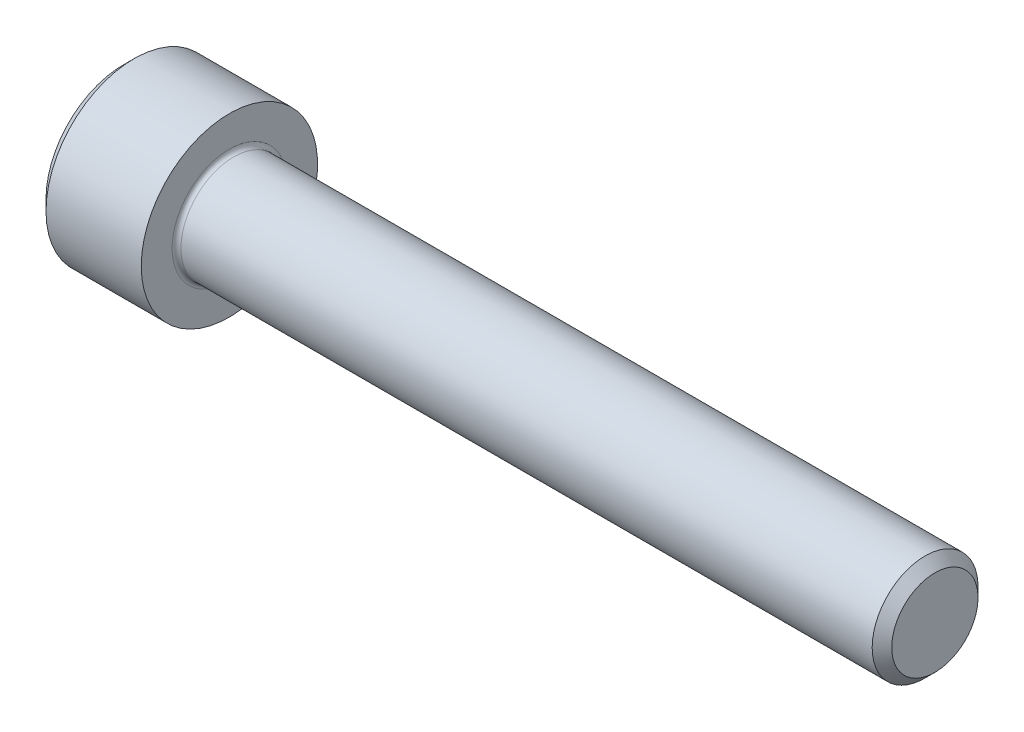
SolidWorks part; units mm, degrees
ref_plane "Plane1" through (0, 0, 0) normal (0, 0, 1) x (1, 0, 0)
ref_plane "Plane2" through (0, 0, 0) normal (0, 1, 0) x (1, 0, 0)
ref_plane "Plane3" through (0, 0, 0) normal (1, 0, 0) x (0, 0, -1)
sketch "BodySke" plane through (0, 0, 0) normal (0, 0, 1) x (1, 0, 0)
  line L0 (0, 0) -> (0, 4.4)
  line L1 (0.6, 5) -> (6, 5)
  line L2 (6, 5) -> (6, 3)
  line L3 (6, 3) -> (45.4455, 3)
  line L4 (46, 2.4455) -> (46, 0)
  line L5 (46, 0) -> (0, 0)
  line L6 (-31.75, 0) -> (127, 0) construction
  line L7 (0, 4.4) -> (0.6, 5)
  line L8 (46, 2.4455) -> (45.4455, 3)
  line L9 (0, -4.4) -> (0.6, -5) construction
  line L10 (46, -2.4455) -> (45.4455, -3) construction
  line L11 (7, 9.525) -> (7, 3.175) construction
  line L12 (22, 9.525) -> (22, 3.175) construction
  line L13 (-4, 9.525) -> (-4, 3.175) construction
  dimension "Diameter" = 6
  dimension "Head_ht" = 6
  dimension "Length" = 40
  dimension "Body_ch_ang" = 45
  dimension "Head_dia" = 10
  dimension "Head_ch_ang" = 45
  dimension "Minor_dia" = 4.891
  dimension "Advance" = 1
  dimension "Thread_nom" = 24
  dimension "Thread_length" = 50
  dimension "Head_ch_ht" = 0.6
revolve "Base-Revolve" add sketch "BodySke"
cosmetic thread "ThreadCosmetic" [suppressed]
fillet "Fillet1" radius 0.25 1 edges at (6, 0, 3)
sketch "Sketch2" plane through (0, 0, 0) normal (0, 0, 1) x (1, 0, 0)
  line L0 (0, 2.542) -> (3, 2.542)
  line L1 (3, 2.542) -> (4.4676, 0)
  line L2 (-31.75, 0) -> (127, 0) construction
  line L3 (4.4676, 0) -> (0, 0)
  line L4 (0, 0) -> (0, 2.542)
  line L5 (0, 4.4) -> (0, -4.4) construction
  line L6 (0, 0) -> (47.625, 0) construction
  line L7 (6, -5) -> (6, 5) construction
  dimension "D1" = 2.542
  dimension "D2" = 60
  dimension "Wall_thickness" = 3
revolve "Hex-PreBroach" cut sketch "Sketch2" angle 360 about L6
sketch "Sketch3" plane through (0, 0, 0) normal (-1, 0, 0) x (0, 0.5, 0.866)
  line L0 (1.4676, 2.542) -> (-1.4676, 2.542)
  line L1 (-1.4676, 2.542) -> (-2.9352, 0)
  line L2 (1.4676, 2.542) -> (2.9352, 0)
  line L3 (1.4676, -2.542) -> (2.9352, 0)
  line L4 (1.4676, -2.542) -> (-1.4676, -2.542)
  line L5 (-1.4676, -2.542) -> (-2.9352, 0)
  dimension "D1" = 2.542
  dimension "D2" = 2.542
  dimension "Hex_size" = 5.084
extrude "Hex" cut sketch "Sketch3" against normal blind 3
sketch "Sketch4" plane through (0, 0, 0) normal (-1, 0, 0) x (0, 0, 1)
  line L0 (0, 0) -> (2.8067, 0)
  line L1 (0, 0) -> (6.1484, 3.5498) construction
  line L2 (0, 0) -> (1.4033, 2.4307)
  line L3 (2.3336, 0.614) -> (2.6851, 0.817)
  line L4 (1.6986, 1.7139) -> (2.0501, 1.9169)
  arc A0 (2.3336, 0.614) -> (1.6986, 1.7139) centre (0, 0) ccw
  arc A1 (2.8067, 0) -> (2.6851, 0.817) centre (0, 0) ccw
  arc A2 (1.4033, 2.4307) -> (2.0501, 1.9169) centre (0, 0) cw
  dimension "D1" = 30
  dimension "Spline_n_dim" = 4.826
  dimension "Spline_m_dim" = 5.6134
  dimension "D2" = 60
  dimension "D3" = 0.635
  dimension "Spline_p_dim" = 1.27
extrude "Spline" [suppressed] cut sketch "Sketch4" against normal blind 3
pattern_circular "CirPattern1" [suppressed] count 6 every 60
sketch "Sketch5" plane through (0, 0, 0) normal (0, 0, 1) x (1, 0, 0)
  line L0 (-31.75, 0) -> (127, 0) construction
  line L2 (0, 4.4) -> (0, -4.4) construction
  circle A0 centre (2.3, 0) radius 0.675
  dimension "Drilled_hole_dia" = 1.35
  dimension "Drilled_hole_loc" = 2.3
extrude "Hole" [suppressed] cut sketch "Sketch5" against normal through all and the other way through all
pattern_circular "Drilled-4" [suppressed] count 2 every 60
pattern_circular "Drilled-6" [suppressed] count 3 every 60
sketch "ThdSchSke" plane through (0, 0, 0) normal (0, 0, 1) x (1, 0, 0)
  line L0 (22, -2.4455) -> (21.6117, -3)
  line L1 (22, -2.4455) -> (22.3883, -3)
  line L2 (22.3883, -3) -> (22.3883, -3.75)
  line L3 (-3.175, 0) -> (5.1513, 0) construction
  line L5 (22.3883, -3.75) -> (21.6117, -3.75)
  line L6 (21.6117, -3.75) -> (21.6117, -3)
  line L7 (0, 4.4) -> (0, -4.4) construction
  dimension "Thread_minor" = 4.891
  dimension "Diameter" = 6
  dimension "Start" = 22
  dimension "SideAngle" = 55
  dimension "VeeAngle" = 70
  dimension "Overcut" = 7.5
revolve "ThreadSchematic" [suppressed] cut sketch "ThdSchSke" angle 360 about L3
pattern_linear "ThdSchPat" [suppressed]
equation "\"D2@Sketch3\" = \"Hex_size@Sketch3\" / 2"
equation "\"D1@Sketch3\" = \"Hex_size@Sketch3\" / 2"
equation "\"D1@Sketch2\" = \"Hex_size@Sketch3\" / 2"
equation "\"D3@Sketch4\" = \"Spline_p_dim@Sketch4\" / 2"
equation "\"Thread_minor@ThreadCosmetic\"  =  \"Minor_dia@BodySke\""
equation "\"D2@CirPattern1\" = 360 / \"Num_teeth@CirPattern1\""
equation "\"Wall_thickness@Sketch2\" = \"Head_ht@BodySke\" - \"Key_eng@Hex\""
equation "\"Thread_length@ThreadCosmetic\" = ((sgn( (\"Length@BodySke\" - \"Advance@BodySke\" ) - \"Thread_nom@BodySke\" )-1)*( (\"Length@BodySke\" - \"Advance@BodySke\" ) - \"Thread_nom@BodySke\" ))/-2+ \"Thread_nom@BodySke\""
equation "\"Thread_minor@ThdSchSke\" = \"Minor_dia@BodySke\""
equation "\"Diameter@ThdSchSke\" = \"Diameter@BodySke\""
equation "\"Overcut@ThdSchSke\" = \"Diameter@BodySke\" * 1.25"
equation "\"Start@ThdSchSke\" = \"Head_ht@BodySke\" + \"Length@BodySke\" - \"Thread_length@ThreadCosmetic\"  '---Non-countersunk---"
equation "\"Num_threads@ThdSchPat\" = int( \"Thread_length@ThreadCosmetic\" / \"Advance@BodySke\" + 0.999 )  + 1"
equation "\"Advance@ThdSchPat\" = \"Thread_length@ThreadCosmetic\" /  (\"Num_threads@ThdSchPat\" - 1) 'relax it"
equation "\"Num_threads@ThdSchPat\" = \"Num_threads@ThdSchPat\" - sgn( \"Num_threads@ThdSchPat\" - 1) '---chamfered tips only---"
